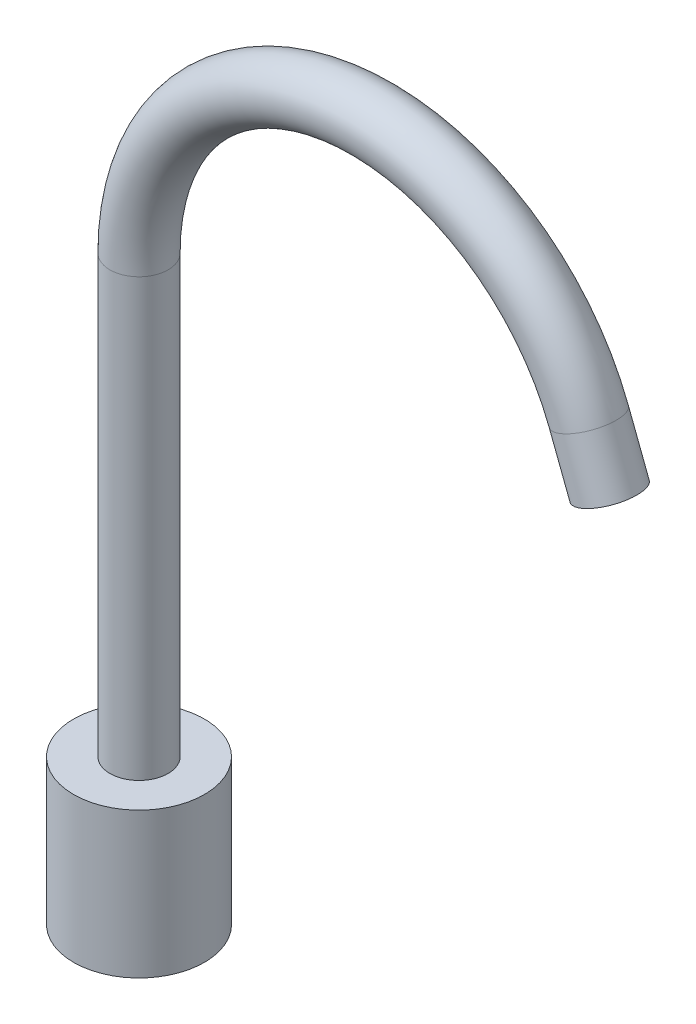
SolidWorks part; units mm, degrees
ref_plane "Спереди" through (0, 0, 0) normal (0, 0, 1) x (1, 0, 0)
ref_plane "Сверху" through (0, 0, 0) normal (0, 1, 0) x (1, 0, 0)
ref_plane "Справа" through (0, 0, 0) normal (1, 0, 0) x (0, 0, -1)
sketch "Эскиз1" plane through (0, 0, 0) normal (0, 0, 1) x (1, 0, 0)
  line L0 (0, 0) -> (0, 200)
  line L1 (154.7032, 228.6256) -> (161.8596, 209.9498)
  arc A0 (0, 200) -> (154.7032, 228.6256) centre (80, 200) cw
  dimension "D2" = 80
  dimension "D1" = 200
  dimension "D3" = 20
sketch "Эскиз2" plane through (0, 0, 0) normal (0, 1, 0) x (1, 0, 0)
  circle A0 centre (0, 0) radius 10
  dimension "D1" = 20
sweep "По траектории1" add profiles "Эскиз2" path "Эскиз1"
sketch "Эскиз3" plane through (0, 0, 0) normal (0, 1, 0) x (1, 0, 0)
  circle A0 centre (0, 0) radius 22.5
  dimension "D1" = 45
extrude "Бобышка-Вытянуть1" add sketch "Эскиз3" along normal blind 50
